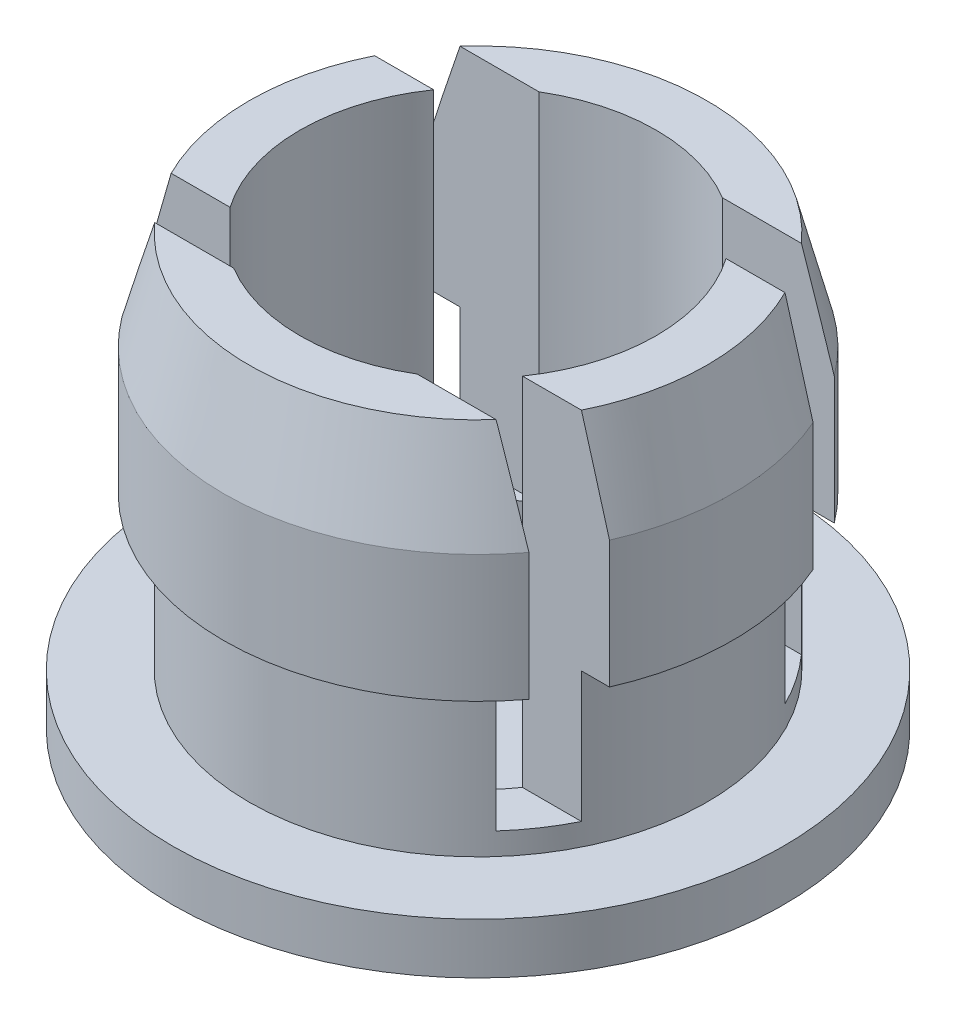
SolidWorks part; units mm, degrees
ref_plane "Alzado" through (0, 0, 0) normal (0, 0, 1) x (1, 0, 0)
ref_plane "Planta" through (0, 0, 0) normal (0, 1, 0) x (1, 0, 0)
ref_plane "Vista lateral" through (0, 0, 0) normal (1, 0, 0) x (0, 0, -1)
sketch "Croquis1" plane through (0, 0, 0) normal (0, 0, 1) x (1, 0, 0)
  line L0 (-78.7823, -15.638) -> (-90.7823, -15.638)
  line L1 (-90.7823, -15.638) -> (-90.7823, -13.638)
  line L2 (-90.7823, -13.638) -> (-87.7823, -13.638)
  line L3 (-87.7823, -13.638) -> (-87.7823, -7.638)
  line L4 (-87.7823, -7.638) -> (-88.7823, -7.638)
  line L5 (-88.7823, -7.638) -> (-88.7823, -2.638)
  line L6 (-88.7823, -2.638) -> (-87.7823, 1.236)
  line L7 (-87.7823, 1.236) -> (-85.7823, 1.236)
  line L8 (-85.7823, 1.236) -> (-85.7823, -13.638)
  line L9 (-85.7823, -13.638) -> (-78.7823, -13.638)
  line L10 (-78.7823, -13.638) -> (-78.7823, -15.638)
revolve "Revolución1" add sketch "Croquis1" angle 360 about L10
sketch "Croquis2" plane through (0, 1.236, 0) normal (0, 1, 0) x (1, 0, 0)
  line L0 (-87.7823, 0) -> (-69.7823, 0) construction
  line L6 (-91.7823, -4) -> (-65.7823, -4)
  line L7 (-91.7823, -4) -> (-91.7823, -6)
  line L8 (-91.7823, -6) -> (-65.7823, -6)
  line L9 (-65.7823, -4) -> (-65.7823, -6)
  line L10 (-91.7823, 4) -> (-65.7823, 4)
  line L11 (-91.7823, 4) -> (-91.7823, 6)
  line L12 (-91.7823, 6) -> (-65.7823, 6)
  line L13 (-65.7823, 4) -> (-65.7823, 6)
  circle A1 centre (-78.7823, 0) radius 9 construction
  dimension "D1" = 2
  dimension "D2" = 2
  dimension "D3" = 4
  dimension "D4" = 4
extrude "Cortar-Extruir1" cut sketch "Croquis2" against normal blind 14
